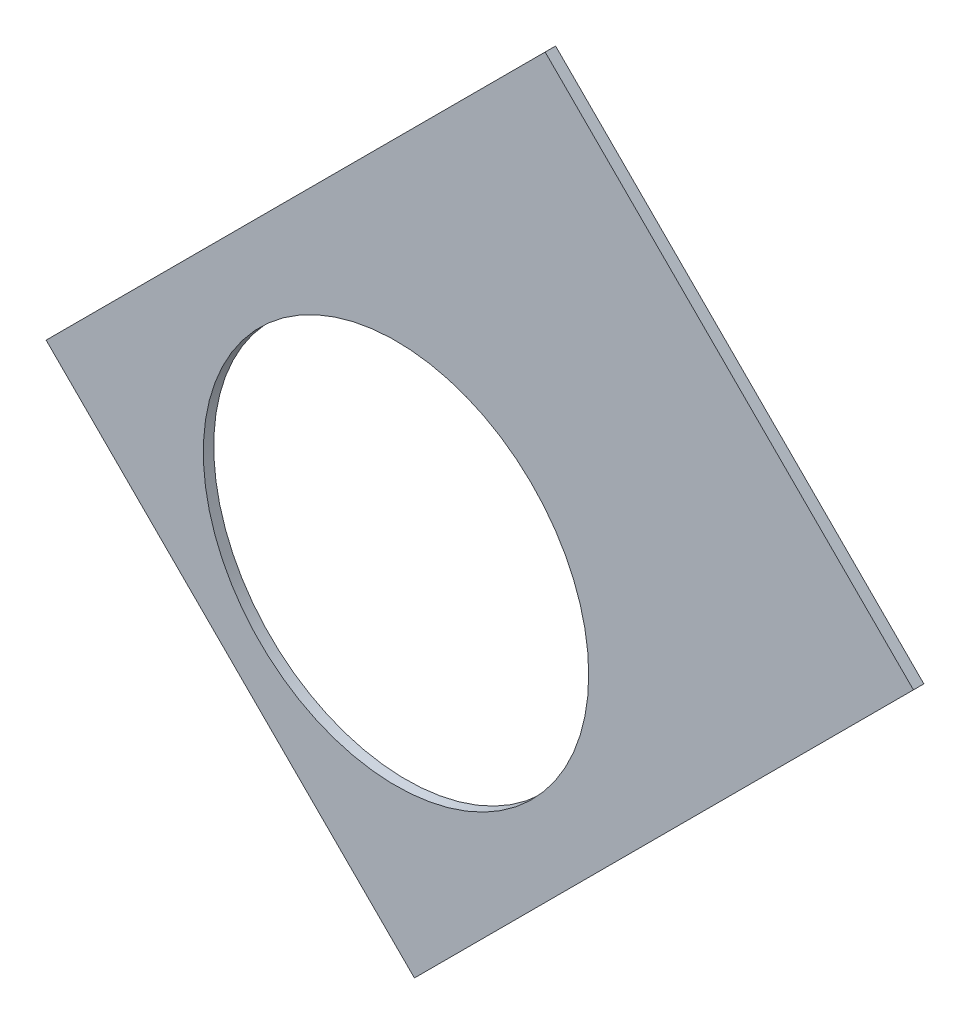
SolidWorks part; units mm, degrees
material "Copper"
ref_plane "Front Plane" through (0, 0, 0) normal (0, 0, 1) x (1, 0, 0)
ref_plane "Top Plane" through (0, 0, 0) normal (0, 1, 0) x (1, 0, 0)
ref_plane "Right Plane" through (0, 0, 0) normal (1, 0, 0) x (0, 0, -1)
sketch "Sketch1" plane through (0, 0, 0) normal (0, 0, 1) x (1, 0, 0)
  line L0 (0, 0) -> (320.3893, 0) construction
  line L1 (0, 0) -> (155.5285, 155.5285) construction
  line L2 (67.2115, 76.1917) -> (8.6967, 17.6769)
  line L3 (8.6967, 17.6769) -> (7.229, 14.1336)
  line L4 (101.4014, -6.35) -> (18.6489, -6.35)
  line L5 (15.1056, -4.8823) -> (18.6489, -6.35)
  line L6 (88.6729, 6.35) -> (27.8605, 6.35)
  line L9 (67.1914, 58.2111) -> (24.1905, 15.2102)
  line L10 (0, 0) -> (40.4486, 97.6516) construction
  line L11 (0, 0) -> (123.4567, -51.1374) construction
  line L18 (8.6967, 17.6769) -> (13.294, 8.6183) construction
  line L19 (18.6489, -6.35) -> (15.4943, 3.3063) construction
  line L20 (27.8605, 6.35) -> (27.7442, 6.7059) construction
  line L21 (24.1905, 15.2102) -> (24.3599, 14.8764) construction
  arc A0 (7.229, 14.1336) -> (15.1056, -4.8823) centre (0, 0) cw
  arc A1 (67.2115, 76.1917) -> (101.4014, -6.35) centre (0, 0) cw
  arc A2 (24.1905, 15.2102) -> (27.8605, 6.35) centre (0, 0) cw
  arc A3 (67.1914, 58.2111) -> (88.6729, 6.35) centre (0, 0) cw
  arc A8 (13.294, 8.6183) -> (15.4943, 3.3063) centre (0, 0) cw construction
  arc A9 (24.3599, 14.8764) -> (27.7442, 6.7059) centre (0, 0) cw construction
  dimension "D1" = 45
  dimension "D3" = 6.35
  dimension "D4" = 15.875
  dimension "D7" = 22.5
  dimension "D8" = 101.6
  dimension "D11" = 12.7
  dimension "D12" = 12.7
  dimension "D2" = 6.35
  dimension "D5" = 67.5
  dimension "D9" = 1.27
  dimension "D10" = 1.27
  dimension "D6" = 12.7
extrude "Boss-Extrude1" add sketch "Sketch1" along normal blind 0.254
sketch "Sketch2" plane through (0, 0, 0.254) normal (0, 0, 1) x (1, 0, 0)
  line L0 (0, 0) -> (101.6, 0) construction
  line L1 (0, 0) -> (71.842, 71.842) construction
  line L3 (0, 0) -> (22.225, 0) construction
  line L4 (0, 0) -> (15.7154, 15.7154) construction
  line L5 (0, 0) -> (95.25, 0) construction
  line L6 (0, 0) -> (92.0044, 24.6525) construction
  arc A0 (101.4014, -6.35) -> (67.2115, 76.1917) centre (0, 0) ccw construction
  circle A1 centre (22.225, 0) radius 4.699
  arc A2 (15.1056, -4.8823) -> (7.229, 14.1336) centre (0, 0) ccw construction
  circle A3 centre (36.195, 0) radius 4.699
  circle A4 centre (61.722, 0) radius 4.699
  circle A5 centre (75.692, 0) radius 4.699
  circle A6 centre (95.25, 0) radius 4.699
  circle A7 centre (15.7154, 15.7154) radius 4.699
  circle A8 centre (25.5937, 25.5937) radius 4.699
  circle A9 centre (43.644, 43.644) radius 4.699
  circle A10 centre (53.5223, 53.5223) radius 4.699
  circle A11 centre (92.0044, 24.6525) radius 4.699
  circle A12 centre (82.4889, 47.625) radius 4.699
  circle A13 centre (67.3519, 67.3519) radius 4.699
  dimension "D3" = 9.398
  dimension "D1" = 45
  dimension "D2" = 6.35
  dimension "D4" = 6.35
  dimension "D5" = 13.97
  dimension "D7" = 13.97
  dimension "D8" = 19.558
  dimension "D9" = 45
  dimension "D10" = 15
  dimension "D11" = 25.527
  dimension "D6" = 2
extrude "Cut-Extrude1" cut sketch "Sketch2" against normal through all
sketch "Sketch3" plane through (0, 0, 0.254) normal (0, 0, 1) x (1, 0, 0)
  line L0 (15.2664, 24.2467) -> (17.0625, 26.0427)
  line L1 (15.2664, 24.2467) -> (15.7154, 23.7977)
  line L2 (17.0625, 26.0427) -> (17.5115, 25.5937)
  line L3 (15.7154, 23.7977) -> (17.5115, 25.5937)
  line L4 (67.2115, 76.1917) -> (8.6967, 17.6769) construction
  line L5 (44.9911, 53.9713) -> (43.195, 52.1753)
  line L6 (44.9911, 53.9713) -> (45.4401, 53.5223)
  line L7 (43.195, 52.1753) -> (43.644, 51.7263)
  line L8 (45.4401, 53.5223) -> (43.644, 51.7263)
  line L9 (27.94, -6.35) -> (30.48, -6.35)
  line L10 (27.94, -6.35) -> (27.94, -5.715)
  line L11 (30.48, -6.35) -> (30.48, -5.715)
  line L12 (27.94, -5.715) -> (30.48, -5.715)
  line L13 (18.6489, -6.35) -> (101.4014, -6.35) construction
  line L14 (67.437, -6.35) -> (69.977, -6.35)
  line L15 (67.437, -6.35) -> (67.437, -5.715)
  line L16 (69.977, -6.35) -> (69.977, -5.715)
  line L17 (67.437, -5.715) -> (69.977, -5.715)
  line L18 (29.2307, 38.211) -> (31.0268, 40.007)
  line L19 (29.2307, 38.211) -> (29.6797, 37.762)
  line L20 (31.0268, 40.007) -> (31.4758, 39.558)
  line L21 (29.6797, 37.762) -> (31.4758, 39.558)
  line L22 (56.845, 65.8253) -> (55.049, 64.0292)
  line L23 (56.845, 65.8253) -> (57.294, 65.3763)
  line L24 (55.049, 64.0292) -> (55.498, 63.5802)
  line L25 (57.294, 65.3763) -> (55.498, 63.5802)
  line L26 (47.6885, -6.35) -> (50.2285, -6.35)
  line L27 (47.6885, -6.35) -> (47.6885, -5.715)
  line L28 (50.2285, -6.35) -> (50.2285, -5.715)
  line L29 (47.6885, -5.715) -> (50.2285, -5.715)
  line L30 (84.201, -6.35) -> (86.741, -6.35)
  line L31 (84.201, -6.35) -> (84.201, -5.715)
  line L32 (86.741, -6.35) -> (86.741, -5.715)
  line L33 (84.201, -5.715) -> (86.741, -5.715)
  line L34 (0, 0) -> (100.7308, 13.2615) construction
  line L35 (0, 0) -> (93.8662, 38.8806) construction
  line L36 (0, 0) -> (80.6047, 61.8502) construction
  line L37 (0, 0) -> (101.6, 0) construction
  line L38 (99.9355, 14.4377) -> (100.267, 11.9194)
  line L39 (99.9355, 14.4377) -> (101.1946, 14.6035)
  line L40 (100.267, 11.9194) -> (101.5261, 12.0852)
  line L41 (101.1946, 14.6035) -> (101.5261, 12.0852)
  line L42 (99.9355, 14.4377) -> (101.5261, 12.0852) construction
  line L43 (100.267, 11.9194) -> (101.1946, 14.6035) construction
  line L44 (93.7655, 37.4643) -> (94.9388, 37.9503)
  line L45 (93.7655, 37.4643) -> (92.7935, 39.811)
  line L46 (94.9388, 37.9503) -> (93.9668, 40.297)
  line L47 (92.7935, 39.811) -> (93.9668, 40.297)
  line L48 (93.7655, 37.4643) -> (93.9668, 40.297) construction
  line L49 (94.9388, 37.9503) -> (92.7935, 39.811) construction
  line L50 (79.3278, 62.4712) -> (80.874, 60.456)
  line L51 (79.3278, 62.4712) -> (80.3354, 63.2443)
  line L52 (80.874, 60.456) -> (81.8816, 61.2292)
  line L53 (80.3354, 63.2443) -> (81.8816, 61.2292)
  line L54 (79.3278, 62.4712) -> (81.8816, 61.2292) construction
  line L55 (80.874, 60.456) -> (80.3354, 63.2443) construction
  line L56 (13.5939, 7.0054) -> (14.5659, 4.6588)
  line L57 (13.5939, 7.0054) -> (14.7672, 7.4914)
  line L58 (14.5659, 4.6588) -> (15.7393, 5.1448)
  line L59 (14.7672, 7.4914) -> (15.7393, 5.1448)
  line L60 (13.5939, 7.0054) -> (15.7393, 5.1448) construction
  line L61 (14.5659, 4.6588) -> (14.7672, 7.4914) construction
  circle A0 centre (15.7154, 15.7154) radius 4.699 construction
  circle A1 centre (43.644, 43.644) radius 4.699 construction
  circle A2 centre (22.225, 0) radius 4.699 construction
  circle A3 centre (61.722, 0) radius 4.699 construction
  arc A4 (101.4014, -6.35) -> (67.2115, 76.1917) centre (0, 0) ccw construction
  arc A9 (15.1056, -4.8823) -> (7.229, 14.1336) centre (0, 0) ccw construction
  circle A10 centre (36.195, 0) radius 4.699 construction
  circle A11 centre (75.692, 0) radius 4.699 construction
  circle A12 centre (25.5937, 25.5937) radius 4.699 construction
  circle A13 centre (53.5223, 53.5223) radius 4.699 construction
  point P75 (14.6666, 6.0751)
  dimension "D2" = 5.715
  dimension "D3" = 2.54
  dimension "D6" = 5.715
  dimension "D8" = 0.635
  dimension "D9" = 5.715
  dimension "D12" = 5.715
  dimension "D4" = 7.5
  dimension "D5" = 22.5
  dimension "D7" = 37.5
  dimension "D10" = 90
  dimension "D11" = 1.27
  dimension "D14" = 0.635
  dimension "D15" = 90
  dimension "D18" = 0.635
  dimension "D19" = 90
  dimension "D22" = 0.635
  dimension "D20" = 1.27
  dimension "D17" = 0.635
  dimension "D13" = 11.4935
  dimension "D16" = 8.509
  dimension "D21" = 11.4935
  dimension "D23" = 8.509
extrude "Cut-Extrude2" cut sketch "Sketch3" against normal through all
sketch "Sketch5" plane through (0, 0, 0.254) normal (0, 0, 1) x (1, 0, 0)
  line L0 (14.3684, 28.7368) -> (26.5367, 40.9051)
  line L4 (14.3684, 28.7368) -> (28.7368, 14.3684)
  line L8 (26.5367, 40.9051) -> (40.9051, 26.5367)
  line L9 (28.7368, 14.3684) -> (40.9051, 26.5367)
  line L12 (15.2664, 24.2467) -> (15.7154, 23.7977) construction
  line L13 (31.4758, 39.558) -> (31.0268, 40.007) construction
  circle A0 centre (25.5937, 25.5937) radius 4.699 construction
  dimension "D1" = 2.54
  dimension "D2" = 2.54
  dimension "D3" = 10.16
  dimension "D4" = 20.32
extrude "Cut-Extrude5" cut sketch "Sketch5" against normal through all flip side to cut
equation "\"cSep\"= 1.005"
equation "\"D11@Sketch2\"=\"cSep\""
equation "\"cSep2\"= \"D8@Sketch2\""
equation "\"D13@Sketch3\"=\"cSep\"/2-.05"
equation "\"D16@Sketch3\"=\"cSep2\"/2-.05"
equation "\"D21@Sketch3\"=\"cSep\"/2-.05"
equation "\"D23@Sketch3\"=\"cSep2\"/2-.05"
